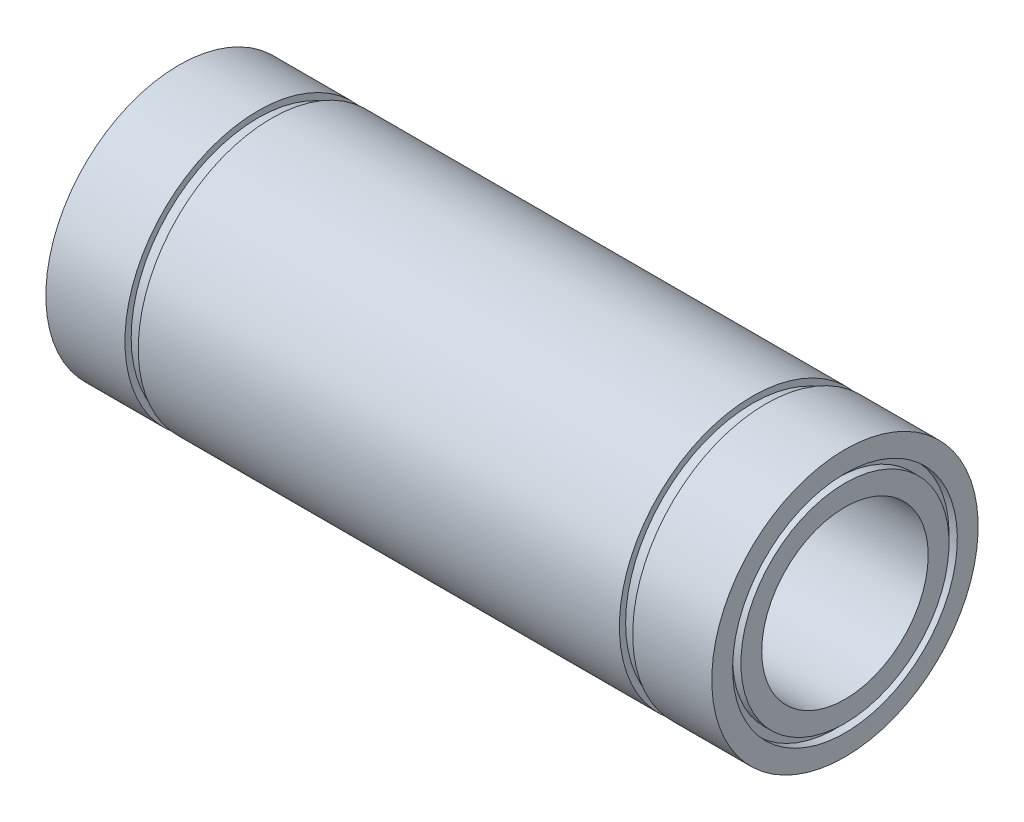
SolidWorks part; units mm, degrees
material "Ст3сп ГОСТ 535-2005"
ref_plane "Plano frontal" through (0, 0, 0) normal (0, 0, 1) x (1, 0, 0)
ref_plane "Plano superior" through (0, 0, 0) normal (0, 1, 0) x (1, 0, 0)
ref_plane "Plano direito" through (0, 0, 0) normal (1, 0, 0) x (0, 0, -1)
sketch "Esboço1" plane through (0, 0, 0) normal (0, 0, 1) x (1, 0, 0)
  line L0 (-40, 16) -> (-30.5, 16)
  line L1 (-30.5, 16) -> (-30.5, 15.25)
  line L2 (-30.5, 15.25) -> (-28.9, 15.25)
  line L3 (-28.9, 15.25) -> (-28.9, 16)
  line L4 (-28.9, 16) -> (28.9, 16)
  line L5 (28.9, 16) -> (28.9, 15.25)
  line L6 (28.9, 15.25) -> (30.5, 15.25)
  line L7 (30.5, 15.25) -> (30.5, 16)
  line L8 (30.5, 16) -> (40, 16)
  line L9 (40, 16) -> (40, 13.5)
  line L10 (40, 10) -> (-40, 10)
  line L11 (-40, 10) -> (-40, 12.5)
  line L12 (0, 10) -> (0, 0) construction
  line L13 (0, 0) -> (-86.5, 0) construction
  line L14 (-40, 13.5) -> (-40, 16)
  line L15 (-40, 13.5) -> (-39, 13.5)
  line L16 (40, 12.5) -> (40, 10)
  line L17 (-39, 13.5) -> (-39, 12.5)
  line L18 (-39, 12.5) -> (-40, 12.5)
  line L19 (40, 13.5) -> (39, 13.5)
  line L21 (40, 12.5) -> (39, 12.5)
  line L22 (39, 13.5) -> (39, 12.5)
  dimension "D1" = 80
  dimension "D2" = 61
  dimension "D3" = 1.6
  dimension "D4" = 20
  dimension "D5" = 32
  dimension "D6" = 30.5
  dimension "D7" = 1
  dimension "D8" = 1
  dimension "D9" = 1
  dimension "D10" = 1
revolve "Revolução1" add sketch "Esboço1" angle 360 about L13
